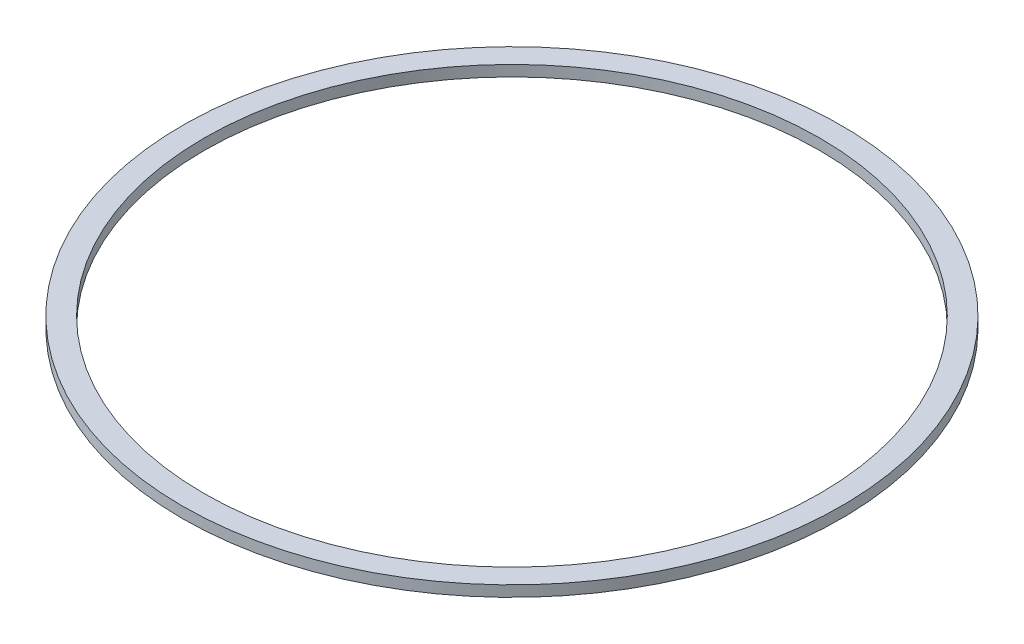
SolidWorks part; units mm, degrees
ref_plane "Front Plane" through (0, 0, 0) normal (0, 0, 1) x (1, 0, 0)
ref_plane "Top Plane" through (0, 0, 0) normal (0, 1, 0) x (1, 0, 0)
ref_plane "Right Plane" through (0, 0, 0) normal (1, 0, 0) x (0, 0, -1)
sketch "Sketch1" plane through (0, 0, 0) normal (0, 1, 0) x (1, 0, 0)
  circle A0 centre (0, 0) radius 75.925
  circle A1 centre (0, 0) radius 70.925
  dimension "D1" = 151.85
  dimension "D2" = 5
extrude "Boss-Extrude1" add sketch "Sketch1" against normal blind 2.5
sketch "Sketch2" plane through (0, -2.5, 0) normal (0, -1, 0) x (1, 0, 0)
  line L0 (0, 0) -> (-50000, 0) construction
  circle A0 centre (0, 0) radius 73.425
  circle A1 centre (0, 0) radius 70.925 construction
  point P3 (-70.925, 0)
  point P6 (-73.425, 0)
  point P9 (-70.925, 0)
  dimension "D1" = 2.5
sweep "Cut-Sweep1" cut path "Sketch2" circular profile diameter 3 parameters "D3"=3
